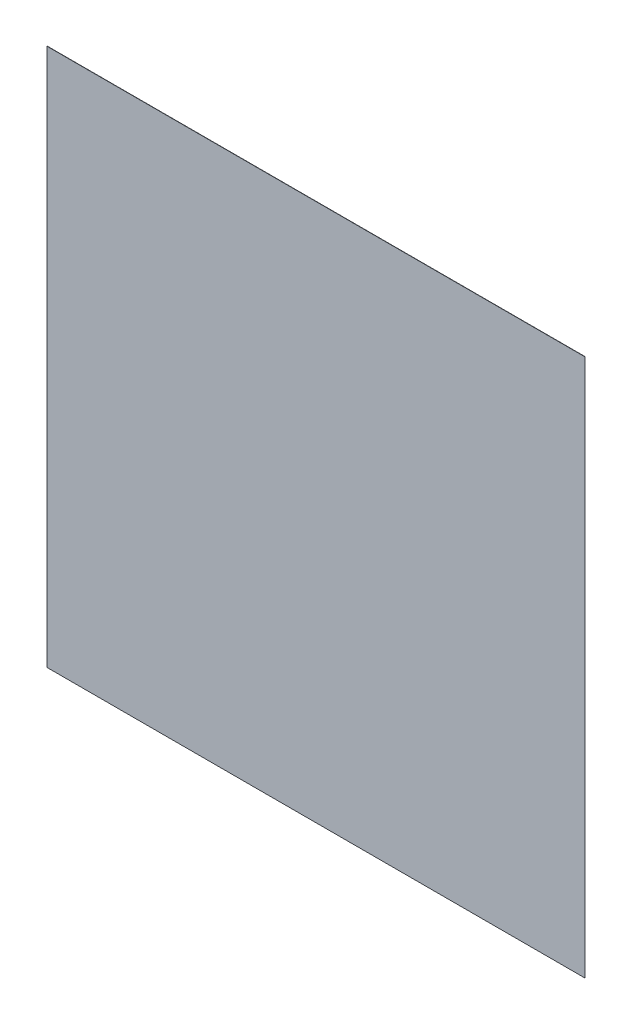
SolidWorks part; units mm, degrees
material "POM Acetal Copolymer"
ref_plane "Front Plane" through (0, 0, 0) normal (0, 0, 1) x (1, 0, 0)
ref_plane "Top Plane" through (0, 0, 0) normal (0, 1, 0) x (1, 0, 0)
ref_plane "Right Plane" through (0, 0, 0) normal (1, 0, 0) x (0, 0, -1)
sketch "Sketch1" plane through (0, 0, 0) normal (0, 0, 1) x (1, 0, 0)
  line L0 (0, 0) -> (0, 101.6) construction
  line L1 (-101.6, 101.6) -> (101.6, 101.6)
  line L2 (-101.6, 101.6) -> (-101.6, -101.6)
  line L3 (-101.6, -101.6) -> (101.6, -101.6)
  line L4 (101.6, 101.6) -> (101.6, -101.6)
  line L5 (0, 0) -> (101.6, 0) construction
  dimension "D1" = 203.2
  dimension "D2" = 203.2
extrude "Boss-Extrude1" add sketch "Sketch1" against normal blind 0.1
